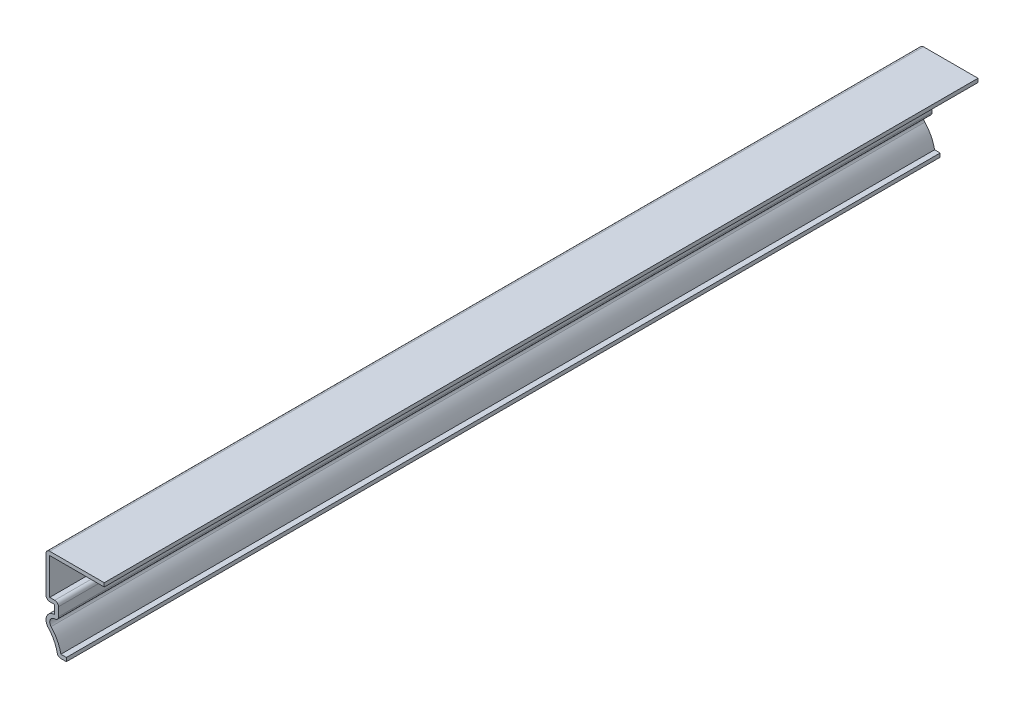
SolidWorks part; units mm, degrees
ref_plane "Front Plane" through (0, 0, 0) normal (0, 0, 1) x (1, 0, 0)
ref_plane "Top Plane" through (0, 0, 0) normal (0, 1, 0) x (1, 0, 0)
ref_plane "Right Plane" through (0, 0, 0) normal (1, 0, 0) x (0, 0, -1)
sketch "Sketch1" plane through (0, 0, 0) normal (0, 0, 1) x (1, 0, 0)
  line L0 (0, 0) -> (0, 23.8125) construction
  line L1 (0, 23.8125) -> (-15.875, 23.8125)
  line L2 (-15.875, 23.8125) -> (-15.875, 11.9062)
  line L3 (-15.875, 11.9062) -> (-13.4938, 11.9062)
  line L4 (-13.4938, 11.9062) -> (-13.4938, 9.525)
  line L5 (-10.3187, 0) -> (-12.7, 0)
  line L6 (-10.3187, 0) -> (0, 0) construction
  arc A0 (-13.4938, 9.525) -> (-15.2293, 5.5133) centre (-13.4938, 7.1437) ccw
  arc A1 (-12.7, 0) -> (-15.2293, 5.5133) centre (-22.1715, -1.0083) ccw
  point P10 (-13.4938, 0.5038)
  point P13 (-13.4938, 5.4352)
  point P14 (-13.8268, 5.6991)
  point P15 (0, 0)
  point P16 (0, 0)
  dimension "D1" = 4.7625
  dimension "D2" = 9.525
  dimension "D3" = 2.3813
  dimension "D4" = 15.875
  dimension "D5" = 2.3813
  dimension "D6" = 2.3813
  dimension "D7" = 11.9062
  dimension "D8" = 23.8125
  dimension "D9" = 3.175
extrude "Extrude-Thin1" add sketch "Sketch1" against normal blind 238.125 thin thin type one direction wall 1.016
fillet "Fillet1" radius 1.016 5 edges at (-12.7, 0, -119.0625) (-12.4778, 8.0557, -119.0625) (-15.875, 11.9062, -119.0625) (-12.4778, 12.9223, -119.0625) (-15.875, 23.8125, -119.0625)
